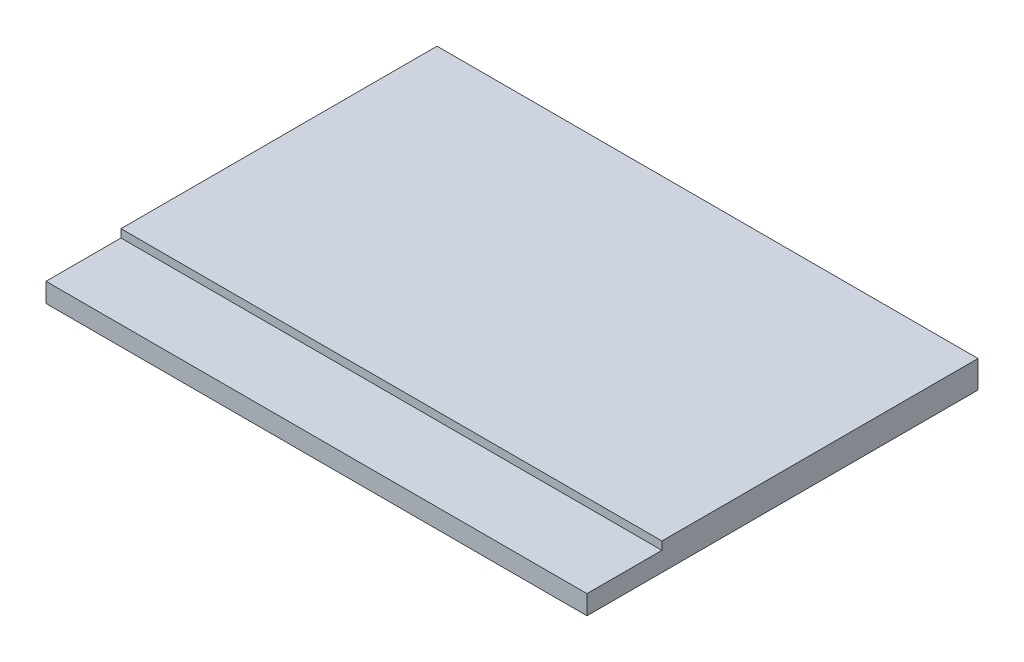
SolidWorks part; units mm, degrees
ref_plane "Front Plane" through (0, 0, 0) normal (0, 0, 1) x (1, 0, 0)
ref_plane "Top Plane" through (0, 0, 0) normal (0, 1, 0) x (1, 0, 0)
ref_plane "Right Plane" through (0, 0, 0) normal (1, 0, 0) x (0, 0, -1)
sketch "Sketch1" plane through (0, 0, 0) normal (0, 1, 0) x (1, 0, 0)
  line L1 (13.35, -9.65) -> (-13.35, -9.65)
  line L2 (13.35, -9.65) -> (13.35, 9.65)
  line L3 (13.35, 9.65) -> (-13.35, 9.65)
  line L4 (-13.35, -9.65) -> (-13.35, 9.65)
  line L5 (13.35, -9.65) -> (-13.35, 9.65) construction
  line L6 (13.35, 9.65) -> (-13.35, -9.65) construction
  point P0 (0, 0)
  dimension "D1" = 26.7
  dimension "D2" = 19.3
extrude "Boss-Extrude1" add sketch "Sketch1" along normal blind 1.35 contours L3 L4 L1 L2
sketch "Sketch2" plane through (0, 1.35, 0) normal (0, 1, 0) x (1, 0, 0)
  line L0 (13.35, -9.65) -> (13.35, 9.65) construction
  line L1 (-13.35, -9.65) -> (13.35, -9.65)
  line L2 (-13.35, -9.65) -> (-13.35, -5.95)
  line L3 (-13.35, -5.95) -> (13.35, -5.95)
  line L4 (13.35, -9.65) -> (13.35, -5.95)
  dimension "D1" = 3.7
extrude "Cut-Extrude1" cut sketch "Sketch2" against normal blind 0.4
